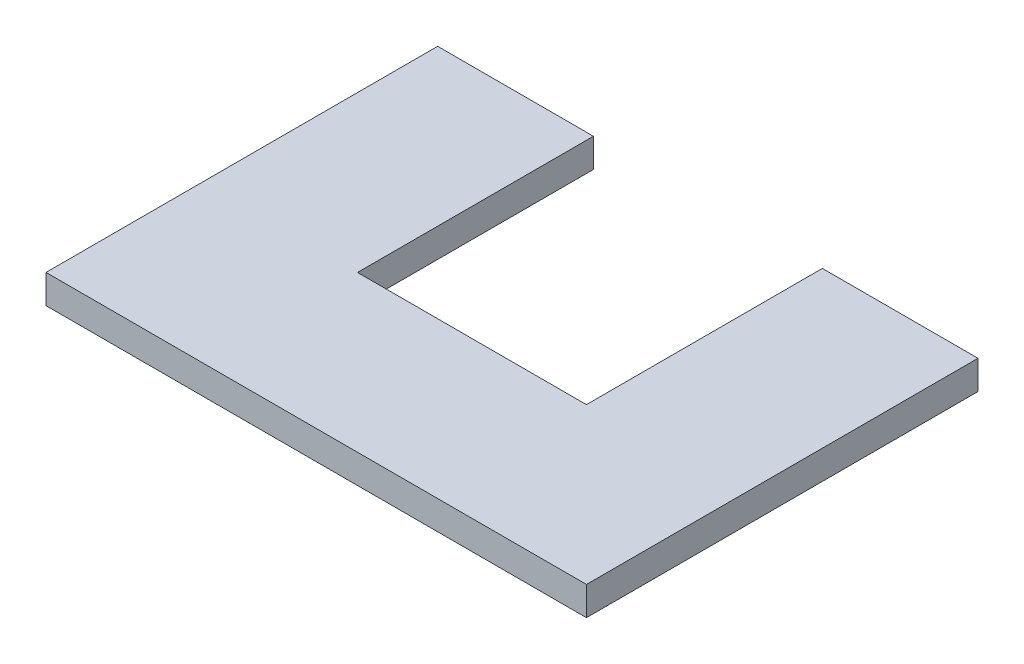
SolidWorks part; units mm, degrees
ref_plane "Front Plane" through (0, 0, 0) normal (0, 0, 1) x (1, 0, 0)
ref_plane "Top Plane" through (0, 0, 0) normal (0, 1, 0) x (1, 0, 0)
ref_plane "Right Plane" through (0, 0, 0) normal (1, 0, 0) x (0, 0, -1)
sketch "Sketch2" plane through (0, 0, 0) normal (0, 1, 0) x (1, 0, 0)
  line L8 (-8.3457, 26.0831) -> (8.8241, 26.0831)
  line L22 (8.8241, 26.0831) -> (8.8241, 0.1689)
  line L24 (8.8241, 0.1689) -> (8.8241, 0.08)
  line L25 (8.8241, 0.08) -> (33.9658, 0.08)
  line L26 (33.9658, 0.08) -> (34.0564, 0.08)
  line L27 (34.0564, 0.08) -> (34.0564, 26.0831)
  line L32 (51.2207, -17.0813) -> (-8.3457, -17.0813)
  line L33 (-8.3457, -17.0813) -> (-8.3457, 26.0831)
  line L34 (34.0564, 26.0831) -> (51.2104, 26.0831)
  line L35 (51.2104, 26.0831) -> (51.2207, -17.0813)
  dimension "D1" = 25.2323
  dimension "D2" = 17.1698
  dimension "D3" = 17.154
  dimension "D4" = 59.5664
  dimension "D5" = 26.0031
  dimension "D6" = 43.1643
  dimension "D7" = 17.1612
extrude "Boss-Extrude1" add sketch "Sketch2" along normal blind 3.175
